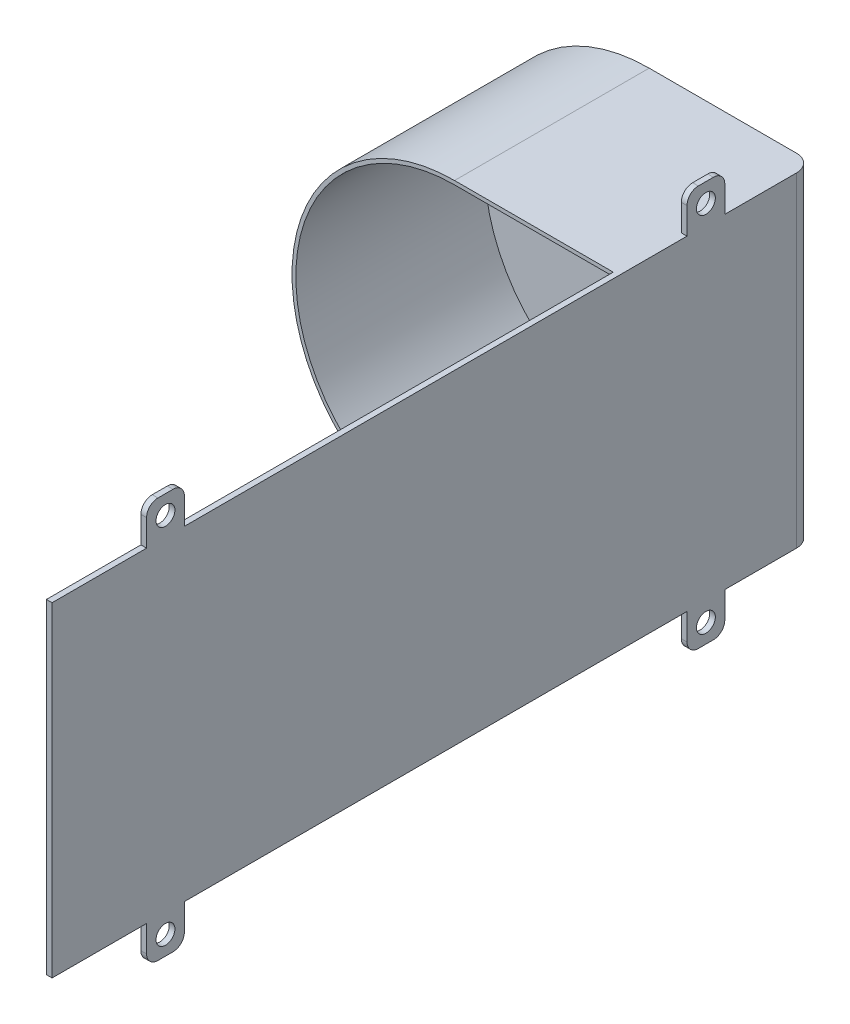
SolidWorks part; units mm, degrees
material "6061-T6 (SS)"
ref_plane "Płaszczyzna przednia" through (0, 0, 0) normal (0, 0, 1) x (1, 0, 0)
ref_plane "Płaszczyzna górna" through (0, 0, 0) normal (0, 1, 0) x (1, 0, 0)
ref_plane "Płaszczyzna prawa" through (0, 0, 0) normal (1, 0, 0) x (0, 0, -1)
sketch "Szkic1" plane through (0, 0, 0) normal (0, 0, 1) x (1, 0, 0)
  line L0 (0, 0) -> (-0.25, 0) construction
  line L1 (-0.25, -43) -> (43.25, -43)
  line L3 (-0.25, 43) -> (43.25, 43)
  line L4 (43.25, -43) -> (43.25, 43)
  line L5 (-43.25, -43) -> (43.25, 43) construction
  line L6 (-43.25, 43) -> (43.25, -43) construction
  circle A0 centre (-0.25, 0) radius 42 construction
  arc A1 (-0.25, 43) -> (-0.25, -43) centre (-0.25, 0) ccw
  point P0 (0, 0)
  dimension "D4" = 84
  dimension "D1" = 86
  dimension "D2" = 86.5
  dimension "D3" = 86
  dimension "D5" = 86.5
  dimension "D6" = 0.25
extrude "Dodanie-wyciągnięcie1" add sketch "Szkic1" along normal blind 1.5
sketch "Szkic2" plane through (0, 0, 1.5) normal (0, 0, 1) x (1, 0, 0)
  line L0 (-0.25, -43) -> (43.25, -43) construction
  line L1 (43.25, 43) -> (41.75, 43)
  line L2 (43.25, 43) -> (43.25, -43)
  line L3 (43.25, -43) -> (41.75, -43)
  line L4 (41.75, 43) -> (41.75, -43)
  dimension "D1" = 1.5
extrude "Dodanie-wyciągnięcie2" add sketch "Szkic2" along normal blind 200
sketch "Szkic4" plane through (0, 0, 1.5) normal (0, 0, 1) x (1, 0, 0)
  line L0 (-0.25, -43) -> (41.75, -43) construction
  line L1 (41.75, 43) -> (-0.25, 43) construction
  line L2 (-0.25, -43) -> (41.75, -43)
  line L3 (41.75, 43) -> (-0.25, 43)
  line L4 (41.75, 42) -> (-0.25, 42)
  line L5 (-0.25, -42) -> (41.75, -42)
  line L6 (41.75, 43) -> (41.75, 42)
  line L7 (41.75, -42) -> (41.75, -43)
  arc A0 (-0.25, 43) -> (-0.25, -43) centre (-0.25, 0) ccw construction
  arc A1 (-0.25, 43) -> (-0.25, -43) centre (-0.25, 0) ccw
  arc A2 (-0.25, 42) -> (-0.25, -42) centre (-0.25, 0) ccw
  dimension "D1" = 1
extrude "Dodanie-wyciągnięcie3" add sketch "Szkic4" along normal blind 50
fillet "Zaokrąglenie1" radius 3 1 edges at (41.75, 0, 1.5)
fillet "Zaokrąglenie2" radius 4.5 1 edges at (43.25, 0, 0)
sketch "Szkic5" plane through (41.75, 0, 0) normal (-1, 0, 0) x (0, 0, 1)
  line L0 (166.5, 43) -> (176.5, 43)
  line L1 (201.5, 43) -> (51.5, 43) construction
  line L2 (176.5, 43) -> (176.5, 50)
  line L3 (173.5, 53) -> (169.5, 53)
  line L4 (166.5, 50) -> (166.5, 43)
  line L5 (201.5, 43) -> (201.5, -43) construction
  line L6 (201.5, 0) -> (103.7453, 0) construction
  line L7 (166.5, -50) -> (166.5, -43)
  line L8 (173.5, -53) -> (169.5, -53)
  line L9 (176.5, -43) -> (176.5, -50)
  line L10 (166.5, -43) -> (176.5, -43)
  arc A0 (169.5, 53) -> (166.5, 50) centre (169.5, 50) ccw
  arc A1 (176.5, 50) -> (173.5, 53) centre (173.5, 50) ccw
  arc A2 (176.5, -50) -> (173.5, -53) centre (173.5, -50) cw
  arc A3 (169.5, -53) -> (166.5, -50) centre (169.5, -50) cw
  point P12 (176.5, 53)
  point P24 (176.5, -53)
  dimension "D4" = 3
  dimension "D1" = 10
  dimension "D2" = 10
  dimension "D3" = 25
extrude "Dodanie-wyciągnięcie4" add sketch "Szkic5" against normal blind 1.5
sketch "Szkic6" plane through (41.75, 0, 0) normal (-1, 0, 0) x (0, 0, 1)
  line L0 (166.5, 43) -> (175.6213, 52.1213) construction
  line L1 (167.3787, 52.1213) -> (176.5, 43) construction
  line L2 (201.5, 0) -> (138.2042, 0) construction
  line L3 (201.5, 43) -> (201.5, -43) construction
  arc A1 (176.5, 50) -> (173.5, 53) centre (173.5, 50) ccw construction
  arc A2 (169.5, 53) -> (166.5, 50) centre (169.5, 50) ccw construction
  circle A3 centre (171.5, 48) radius 2.5
  circle A4 centre (171.5, -48) radius 2.5
  dimension "D1" = 5
extrude "Wytnij-wyciągnięcie1" cut sketch "Szkic6" against normal through all
ref_plane "Płaszczyzna1" through (0, 0, 191.5) normal (0, 0, 1) x (1, 0, 0)
ref_plane "Płaszczyzna2" through (0, 0, 21.5) normal (0, 0, 1) x (1, 0, 0)
ref_plane "Płaszczyzna3" through (0, 0, 100) normal (0, 0, 1) x (1, 0, 0)
mirror "Lustro1" about plane through (0, 0, 100) normal (0, 0, 1) of "Wytnij-wyciągnięcie1", "Dodanie-wyciągnięcie4"
